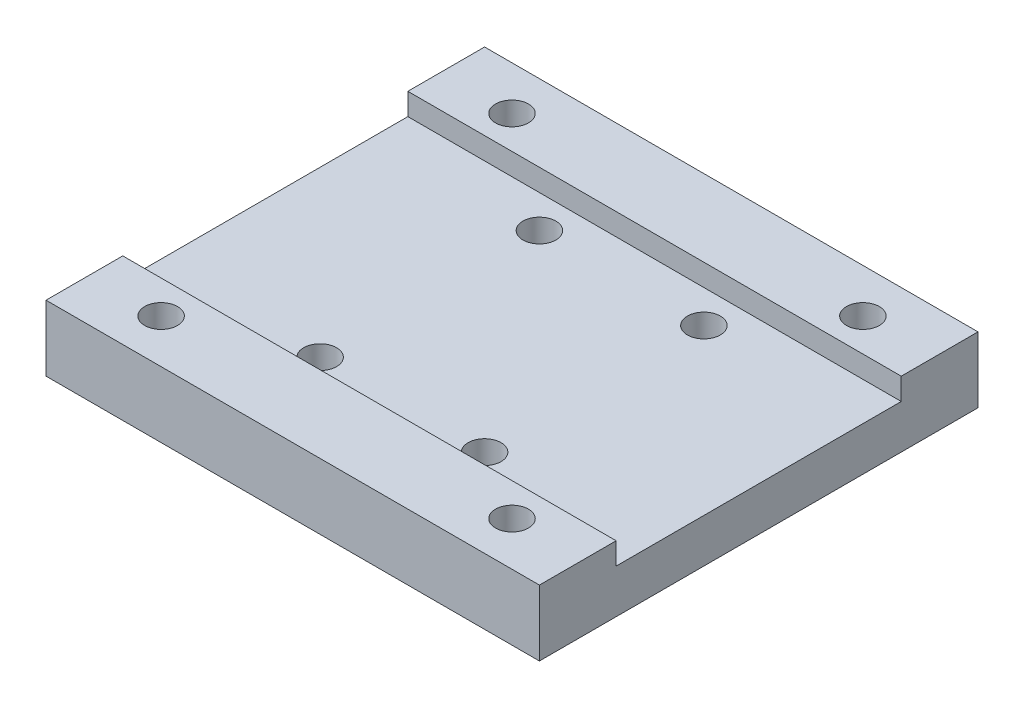
SolidWorks part; units mm, degrees
material "6063-O"
ref_plane "前视基准面" through (0, 0, 0) normal (0, 0, 1) x (1, 0, 0)
ref_plane "上视基准面" through (0, 0, 0) normal (0, 1, 0) x (1, 0, 0)
ref_plane "右视基准面" through (0, 0, 0) normal (1, 0, 0) x (0, 0, -1)
sketch "草图2" plane through (0, 0, 0) normal (0, 1, 0) x (1, 0, 0)
  line L0 (-313.7764, 0) -> (366.0313, 0) construction
  line L1 (0, 306.7192) -> (0, -276.9347) construction
  line L2 (-22.5, 16.5) -> (-22.5, -16.5)
  line L3 (-22.5, -16.5) -> (22.5, -16.5)
  line L4 (22.5, -16.5) -> (22.5, 16.5)
  line L5 (22.5, 16.5) -> (-22.5, 16.5)
  circle A0 centre (-7.5, 10) radius 1.5
  circle A1 centre (7.5, 10) radius 1.5
  circle A2 centre (-7.5, -10) radius 1.5
  circle A3 centre (7.5, -10) radius 1.5
  dimension "D3" = 3
  dimension "D1" = 33
  dimension "D2" = 45
  dimension "D4" = 15
  dimension "D5" = 20
extrude "凸台-拉伸1" add sketch "草图2" along normal blind 6
sketch "草图3" plane through (0, 0, 0) normal (0, -1, 0) x (1, 0, 0)
  line L0 (22.5, -16.5) -> (-22.5, -16.5)
  line L1 (22.5, 16.5) -> (22.5, -16.5) construction
  line L2 (-22.5, -16.5) -> (-22.5, 16.5) construction
  line L3 (-22.5, -16.5) -> (-22.5, -20)
  line L4 (-22.5, -20) -> (22.5, -20)
  line L5 (22.5, -20) -> (22.5, -16.5)
  line L6 (22.5, 20) -> (-22.5, 20)
  line L7 (-22.5, 20) -> (-22.5, 16.5)
  line L8 (-22.5, 16.5) -> (22.5, 16.5)
  line L9 (22.5, 16.5) -> (22.5, 20)
  line L11 (22.5, -16.5) -> (-22.5, -16.5) construction
  line L12 (-22.5, 16.5) -> (22.5, 16.5) construction
  dimension "D1" = 3.5
  dimension "D2" = 3.5
extrude "凸台-拉伸2" add sketch "草图3" against normal blind 6
sketch "草图9" plane through (0, 6, 0) normal (0, 1, 0) x (1, 0, 0)
  line L0 (-6.025, 20) -> (-6.025, 16.5)
  line L1 (-22.5, 20) -> (22.5, 20) construction
  line L2 (-6.025, 16.5) -> (6.025, 16.5)
  line L3 (6.025, 16.5) -> (6.025, 20)
  line L4 (-34.8663, 0) -> (36.5419, 0) construction
  line L5 (0, 26.3212) -> (0, -26.6147) construction
  line L6 (6.025, 20) -> (-6.025, 20)
  line L7 (6.025, -20) -> (-6.025, -20)
  line L8 (6.025, -16.5) -> (6.025, -20)
  line L9 (-6.025, -16.5) -> (6.025, -16.5)
  line L10 (-6.025, -20) -> (-6.025, -16.5)
  dimension "D1" = 12.05
  dimension "D2" = 33
extrude "切除-拉伸2" [suppressed] cut sketch "草图9" against normal up to next
chamfer "倒角1" [suppressed] distance 0.5 angle 45
sketch "草图20" plane through (0, 6, 0) normal (0, 1, 0) x (1, 0, 0)
  line L0 (35.9387, 0) -> (-46.2221, 0) construction
  line L1 (0, -31.7132) -> (0, 31.5639) construction
  line L2 (22.5, -13.75) -> (-22.5, -13.75)
  line L3 (-22.5, -13.75) -> (-22.5, 13.75)
  line L4 (-22.5, 13.75) -> (22.5, 13.75)
  line L5 (22.5, 13.75) -> (22.5, -13.75)
  line L6 (22.5, -20) -> (22.5, 20) construction
  line L7 (-22.5, 20) -> (-22.5, -20) construction
  dimension "D1" = 27.5
extrude "切除-拉伸5" cut sketch "草图20" against normal blind 2
sketch "草图21" plane through (0, 4, 0) normal (0, -1, 0) x (1, 0, 0)
  line L0 (22.5, -16.5) -> (-22.5, -16.5)
  line L1 (-22.5, -16.5) -> (-22.5, -13)
  line L2 (-22.5, -20) -> (-22.5, 20) construction
  line L3 (-22.5, -13) -> (22.5, -13)
  line L4 (22.5, 20) -> (22.5, -20) construction
  line L5 (22.5, -13) -> (22.5, -16.5)
  line L6 (-22.5, 16.5) -> (22.5, 16.5)
  line L7 (22.5, 16.5) -> (22.5, 13)
  line L8 (22.5, 13) -> (-22.5, 13)
  line L9 (-22.5, 13) -> (-22.5, 16.5)
  line L12 (-22.5, -13.75) -> (-22.5, 13.75) construction
  line L13 (22.5, 13.75) -> (22.5, -13.75) construction
  line L14 (-43.6059, 0) -> (39.6984, 0) construction
  line L15 (22.5, 20) -> (-22.5, 20) construction
  dimension "D1" = 7
extrude "凸台-拉伸3" add sketch "草图21" along normal up to surface (2 mm away)
hole_wizard "Ø3.0 (3) 直径孔1" positions "草图22" profile "草图23" hole size "Ø3.0" standard "GB" end condition up to next
sketch "草图22" plane through (0, 6, 0) normal (0, 1, 0) x (1, 0, 0)
  line L1 (-313.7764, 0) -> (366.0313, 0) construction
  line L2 (0, 306.7192) -> (0, -276.9347) construction
  line L3 (-313.7764, 0) -> (366.0313, 0) construction
  line L4 (0, 306.7192) -> (0, -276.9347) construction
  point P0 (-16, 16)
  point P2 (16, 16)
  point P4 (16, -16)
  point P6 (-16, -16)
  dimension "D1" = 32
  dimension "D2" = 32
sketch "草图23" plane through (-16, 6, -16) normal (1, 0, 0) x (0, 0, 1)
  line L0 (0, 0) -> (0, 6)
  line L1 (0, 6) -> (1.5, 6)
  line L2 (1.5, 6) -> (1.5, 0)
  line L5 (1.5, 0) -> (0, 0)
  line L11 (0, -6.35) -> (0, 107.95) construction
  dimension "通孔孔直径" = 3
  dimension "通孔孔深度" = 6
hole_wizard "M3 螺纹孔2" positions "草图24" profile "草图25" tap size "M3" standard "GB"
sketch "草图24" plane through (0, 0, 0) normal (0, -1, 0) x (-1, 0, 0)
  line L0 (313.7764, 0) -> (-366.0313, 0) construction
  line L1 (0, 306.7192) -> (0, -276.9347) construction
  line L2 (313.7764, 0) -> (-366.0313, 0) construction
  line L3 (0, 306.7192) -> (0, -276.9347) construction
  line L4 (-22.5, -20) -> (22.5, -20) construction
  point P0 (3.5, -17)
  point P2 (-3.5, -17)
  point P4 (-3.5, 17)
  point P6 (3.5, 17)
  dimension "D1" = 3
  dimension "D2" = 7
cosmetic thread "孔螺蚊线5" parameters "D1"=4, "D2"=3
cosmetic thread "孔螺蚊线6" parameters "D1"=4, "D2"=3
cosmetic thread "孔螺蚊线7" parameters "D1"=4, "D2"=3
cosmetic thread "孔螺蚊线8" parameters "D1"=4, "D2"=3
sketch "草图25" plane through (-3.5, 0, 17) normal (1, 0, 0) x (0, 0, -1)
  line L0 (0, 0) -> (0, 4.7511)
  line L1 (0, 4.7511) -> (1.25, 4)
  line L2 (1.25, 4) -> (1.25, 0)
  line L5 (1.25, 0) -> (0, 0)
  line L10 (0, 4.7511) -> (-1.25, 4) construction
  line L11 (0, -6.35) -> (0, 107.95) construction
  dimension "螺纹孔钻头直径" = 2.5
  dimension "螺纹孔钻头深度" = 4
  dimension "导头角度" = 118
hole_wizard "打孔尺寸(%根据)内六角圆柱头螺钉的类型1" positions "草图26" profile "草图27" counterbore size "M3" standard "GB" end condition up to next
sketch "草图26" plane through (0, 0, 0) normal (0, -1, 0) x (-1, 0, 0)
  point P0 (-16, 16)
  point P3 (16, 16)
  point P6 (16, -16)
  point P9 (-16, -16)
sketch "草图27" plane through (16, 0, -16) normal (1, 0, 0) x (0, 0, -1)
  line L0 (0, 0) -> (0, 6)
  line L1 (0, 6) -> (1.5, 6)
  line L3 (1.5, 6) -> (1.5, 3)
  line L4 (1.5, 3) -> (3, 3)
  line L5 (3, 3) -> (3, 0)
  line L7 (3, 0) -> (0, 0)
  line L11 (0, -6.35) -> (0, 107.95) construction
  dimension "通孔孔直径" = 3
  dimension "通孔孔深度" = 6
  dimension "柱形沉头孔直径" = 6
  dimension "柱形沉头孔深度" = 3
